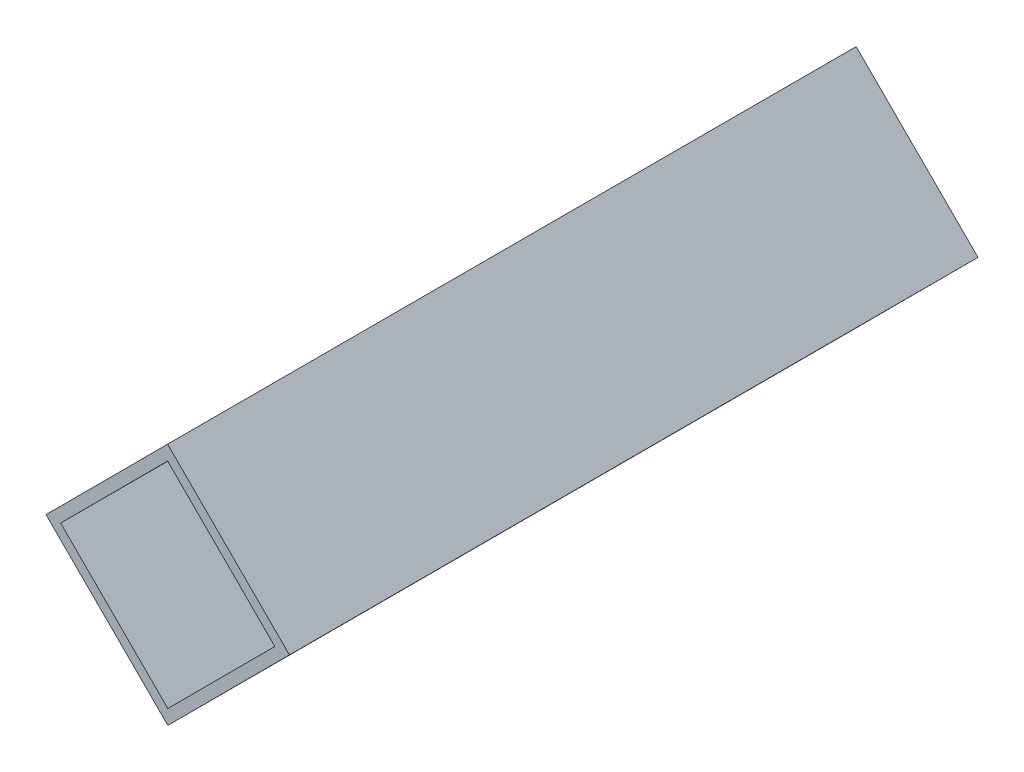
SolidWorks part; units mm, degrees
material "可鍛鑄鐵"
ref_plane "前基準面" through (0, 0, 0) normal (0, 0, 1) x (1, 0, 0)
ref_plane "上基準面" through (0, 0, 0) normal (0, 1, 0) x (1, 0, 0)
ref_plane "右基準面" through (0, 0, 0) normal (1, 0, 0) x (0, 0, -1)
sketch "草圖1" plane through (0, 0, 0) normal (0, 0, 1) x (1, 0, 0)
  line L0 (0, 0) -> (17.6938, -17.6615)
  line L1 (0, 0) -> (-17.6615, -17.6938)
  line L2 (17.6938, -17.6615) -> (0.0323, -35.3553)
  line L3 (-17.6615, -17.6938) -> (0.0323, -35.3553)
  line L4 (0.0019, -2.1213) -> (-15.5402, -17.6919)
  line L5 (0.0019, -2.1213) -> (15.5725, -17.6635)
  line L6 (-15.5402, -17.6919) -> (0.0303, -33.234)
  line L7 (15.5725, -17.6635) -> (0.0303, -33.234)
  point P0 (8.8469, -8.8308)
  dimension "D1" = 25
  dimension "D2" = 25
  dimension "D3" = 1.5
  dimension "D4" = 1.5
  dimension "D5" = 1.5
  dimension "D6" = 1.5
extrude "填料-伸長1" add sketch "草圖1" along normal blind 100
sketch "草圖2" plane through (0, 0, 0) normal (0.7065, 0.7078, 0) x (0.7078, -0.7065, 0)
  line L0 (25, -100) -> (0, -100) construction
  line L1 (25, -100) -> (25, 0) construction
  line L2 (25, 0) -> (0, 0) construction
  line L3 (0, -100) -> (0, 0) construction
  circle A0 centre (12.5, 72) radius 2.75
  circle A1 centre (12.5, 28) radius 2.75
  circle A2 centre (12.5, -128) radius 2.75
  circle A3 centre (12.5, -172) radius 2.75
  dimension "D1" = 5.5
  dimension "D2" = 5.5
  dimension "D4" = 128
  dimension "D5" = 12.5
  dimension "D6" = 12.5
  dimension "D7" = 5.5
  dimension "D8" = 5.5
  dimension "D9" = 44
  dimension "D10" = 128
  dimension "D11" = 12.5
  dimension "D3" = 44
